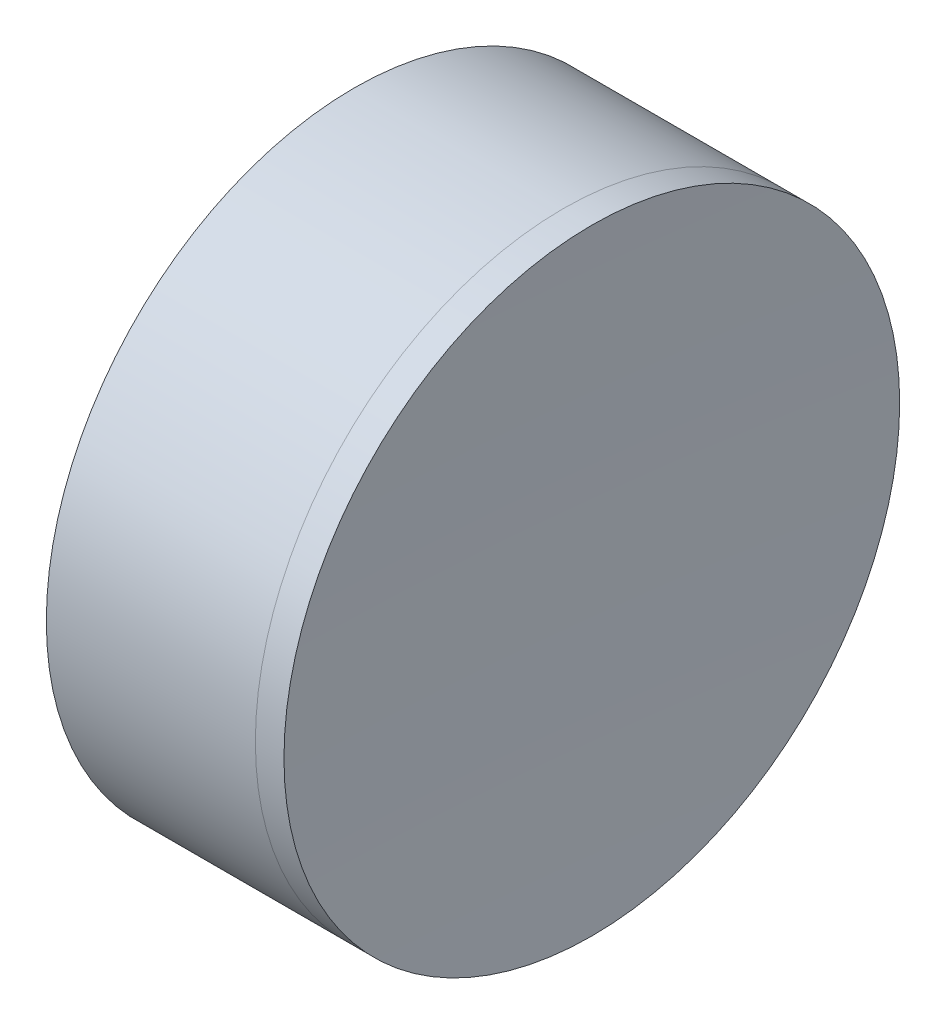
SolidWorks part; units mm, degrees
ref_plane "前视基准面" through (0, 0, 0) normal (0, 0, 1) x (1, 0, 0)
ref_plane "上视基准面" through (0, 0, 0) normal (0, 1, 0) x (1, 0, 0)
ref_plane "右视基准面" through (0, 0, 0) normal (1, 0, 0) x (0, 0, -1)
sketch "草图1" plane through (0, 0, 0) normal (0, 1, 0) x (1, 0, 0)
  line L0 (-185.2745, 0) -> (449.3721, 0) construction
  line L1 (152.9183, 12.7) -> (161.5418, 12.7)
  line L4 (152.9183, -12.7) -> (161.5418, -12.7)
  arc A0 (152.9183, -12.7) -> (152.9183, 12.7) centre (132.0488, 0) ccw
  arc A1 (161.5418, 12.7) -> (161.5418, -12.7) centre (186.3388, 0) ccw
  point P6 (156.4788, 0)
  point P8 (158.4788, 0)
  dimension "D3" = 12.7
  dimension "D4" = 2
  dimension "D1" = 24.43
  dimension "D5" = 27.86
  dimension "D2" = 12.7
revolve "旋转1" add sketch "草图1" angle 360 about L0
sketch "草图2" plane through (0, 0, 0) normal (0, 1, 0) x (1, 0, 0)
  line L2 (152.9183, 0) -> (272.9951, 0) construction
  line L3 (152.9183, -12.7) -> (152.9183, 12.7) construction
  line L6 (161.5418, 12.7) -> (162.7216, 12.7)
  line L7 (161.5418, -12.7) -> (162.7216, -12.7)
  arc A2 (161.5418, 12.7) -> (161.5418, -12.7) centre (186.3388, 0) ccw construction
  arc A3 (161.5418, 12.7) -> (161.5418, -12.7) centre (186.3388, 0) ccw
  arc A4 (162.7216, 12.7) -> (162.7216, -12.7) centre (494.7788, 0) ccw
  point P8 (158.4788, 0)
  point P9 (162.4788, 0)
  dimension "D1" = 4
  dimension "D2" = 332.3
revolve "旋转3" add sketch "草图2" angle 360 about L2
